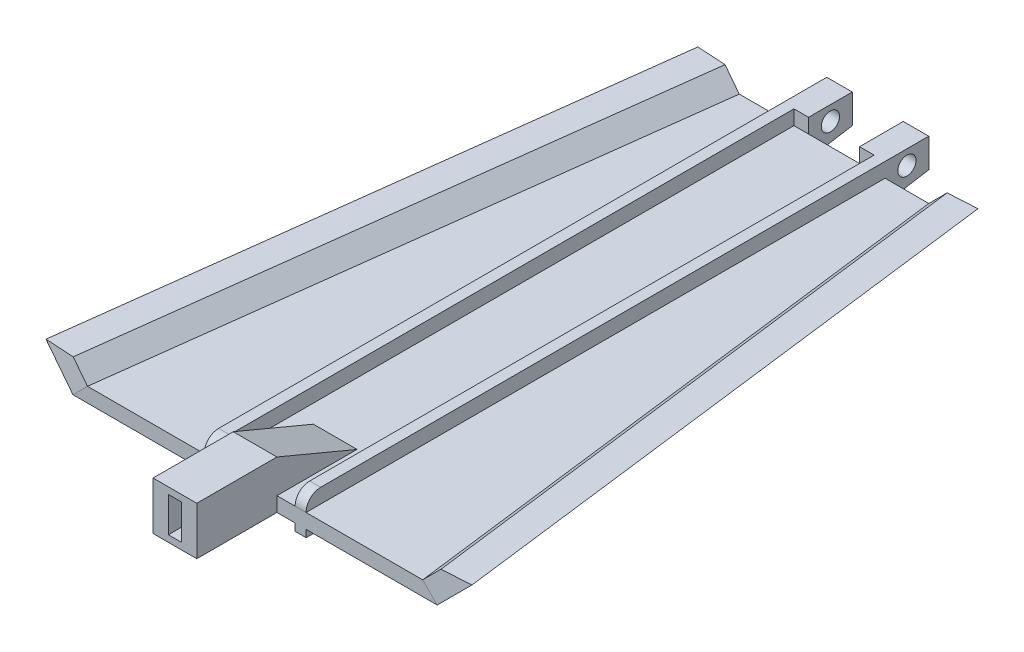
SolidWorks part; units mm, degrees
ref_plane "Front Plane" through (0, 0, 0) normal (0, 0, 1) x (1, 0, 0)
ref_plane "Top Plane" through (0, 0, 0) normal (0, 1, 0) x (1, 0, 0)
ref_plane "Right Plane" through (0, 0, 0) normal (1, 0, 0) x (0, 0, -1)
sketch "Sketch1" plane through (0, 0, 0) normal (0, 1, 0) x (1, 0, 0)
  line L4 (-21.0586, -39.6541) -> (28.9414, -39.6541)
  line L9 (-26.3294, 36.0752) -> (28.9414, -39.6541) construction
  line L10 (-21.0586, -39.6541) -> (22.9141, 43.1481) construction
  line L11 (28.9414, -39.6541) -> (18.9414, 39.805)
  line L12 (18.9414, 39.805) -> (-11.0586, 39.805)
  line L13 (-11.0586, 39.805) -> (-21.0586, -39.6541)
  point P0 (0, 0)
  dimension "D1" = 50
  dimension "D2" = 30
extrude "Boss-Extrude1" add sketch "Sketch1" along normal blind 2
sketch "Sketch2" plane through (0, 0, 39.6541) normal (0, 0, 1) x (1, 0, 0)
  line L0 (-21.0586, 2) -> (-21.0586, 0)
  line L1 (-21.0586, 0) -> (-19.0586, 2)
  line L2 (-21.0586, 2) -> (28.9414, 2) construction
  line L3 (-19.0586, 2) -> (-21.0586, 2)
sketch "Sketch3" plane through (0, 0, -39.805) normal (0, 0, -1) x (-1, 0, 0)
  line L2 (-18.9414, 2) -> (11.0586, 2) construction
  line L4 (11.0586, 0) -> (11.0586, 2)
  line L5 (11.0586, 2) -> (9.0586, 2)
  line L6 (9.0586, 2) -> (11.0586, 0)
  dimension "D2" = 2
loft "Cut-Loft1" cut profiles "Sketch2", "Sketch3"
sketch "Sketch4" plane through (0, 0, 39.6541) normal (0, 0, 1) x (1, 0, 0)
  line L0 (28.9414, 0) -> (28.9414, 2)
  line L1 (28.9414, 2) -> (26.9414, 2)
  line L2 (-19.0586, 2) -> (28.9414, 2) construction
  line L3 (26.9414, 2) -> (28.9414, 0)
  dimension "D1" = 2
sketch "Sketch5" plane through (0, 0, -39.805) normal (0, 0, -1) x (-1, 0, 0)
  line L0 (-18.9414, 0) -> (-18.9414, 2)
  line L1 (-18.9414, 2) -> (-16.9414, 2)
  line L2 (-18.9414, 2) -> (9.0586, 2) construction
  line L3 (-16.9414, 2) -> (-18.9414, 0)
  dimension "D1" = 2
loft "Cut-Loft2" cut profiles "Sketch5", "Sketch4"
sketch "Sketch6" plane through (11.8814, 11.8814, -1.4953) normal (0.7043, 0.7043, -0.0886) x (-0.0627, -0.0627, -0.9961)
  line L0 (-41.312, -20.4647) -> (38.4611, -13.3936)
  line L1 (38.4611, -13.3936) -> (38.4611, -10.5652)
  line L2 (38.4611, -10.5652) -> (-41.312, -17.6362)
  line L3 (-41.312, -17.6362) -> (-41.312, -20.4647)
extrude "Boss-Extrude2" add sketch "Sketch6" along normal blind 6
sketch "Sketch7" plane through (-7.9709, 7.9709, -1.0031) normal (-0.7043, 0.7043, -0.0886) x (-0.0627, 0.0627, 0.9961)
  line L0 (-38.9552, -4.9912) -> (40.8179, -12.0622)
  line L1 (40.8179, -12.0622) -> (40.8179, -14.8907)
  line L2 (40.8179, -14.8907) -> (-38.9552, -7.8196)
  line L3 (-38.9552, -7.8196) -> (-38.9552, -4.9912)
extrude "Boss-Extrude3" add sketch "Sketch7" along normal blind 6
sketch "Sketch8" plane through (-2.5584, 2.5584, 40.6573) normal (-0.0627, 0.0627, 0.9961) x (0.998, 0.0039, 0.0626)
  line L4 (-22.7709, 1.7607) -> (-18.7788, 1.7607)
  line L5 (-20.767, 3.7567) -> (-16.5327, -0.4943) construction
  line L6 (-18.7788, 1.7607) -> (-20.767, 3.7567)
  line L7 (-20.767, 3.7567) -> (-22.7709, 1.7607)
sketch "Sketch9" plane through (2.4416, -2.4416, -38.8019) normal (0.0627, -0.0627, -0.9961) x (-0.998, -0.0039, -0.0626)
  line L4 (17.7611, 6.7508) -> (13.7689, 6.7508)
  line L5 (15.7571, 8.7469) -> (11.5229, 4.4959) construction
  line L6 (13.7689, 6.7508) -> (15.7571, 8.7469)
  line L7 (15.7571, 8.7469) -> (17.7611, 6.7508) construction
  line L8 (15.7571, 8.7469) -> (17.7611, 6.7508)
loft "Cut-Loft3" cut profiles "Sketch9", "Sketch8"
sketch "Sketch12" plane through (-2.4107, -2.4107, -38.3097) normal (-0.0627, -0.0627, -0.9961) x (-0.998, 0.0039, 0.0626)
  line L0 (-25.6284, 6.7508) -> (-21.6363, 6.7508)
  line L1 (-23.6245, 8.7469) -> (-19.3902, 4.4959) construction
  line L2 (-21.6363, 6.7508) -> (-23.6245, 8.7469)
  line L3 (-23.6245, 8.7469) -> (-25.6284, 6.7508)
sketch "Sketch13" plane through (2.5893, 2.5893, 41.1494) normal (0.0627, 0.0627, 0.9961) x (0.998, -0.0039, -0.0626)
  line L0 (30.6383, 1.7607) -> (26.6461, 1.7607)
  line L1 (28.6343, 3.7567) -> (24.4, -0.4943) construction
  line L2 (26.6461, 1.7607) -> (28.6343, 3.7567)
  line L3 (28.6343, 3.7567) -> (30.6383, 1.7607)
loft "Cut-Loft4" cut profiles "Sketch13", "Sketch12"
sketch "Sketch14" plane through (0, 2, 0) normal (0, 1, 0) x (1, 0, 0)
  line L0 (3.9414, 39.805) -> (3.9414, -39.6541) construction
  line L1 (16.9414, 39.805) -> (-9.0586, 39.805) construction
  line L2 (-19.0586, -39.6541) -> (26.9414, -39.6541) construction
  line L3 (3.9414, 39.805) -> (9.4414, 39.805) construction
  line L4 (3.9414, 39.805) -> (-1.5586, 39.805) construction
  line L5 (9.4414, 39.805) -> (9.4414, -39.6541)
  line L6 (-1.5586, 39.805) -> (-1.5586, -39.6541)
  line L7 (-1.5586, -39.6541) -> (-3.0586, -39.6541)
  line L8 (-3.0586, -39.6541) -> (-3.0586, 39.805)
  line L9 (-3.0586, 39.805) -> (-1.5586, 39.805)
  line L10 (9.4414, 39.805) -> (10.9414, 39.805)
  line L11 (10.9414, 39.805) -> (10.9414, -39.6541)
  line L12 (10.9414, -39.6541) -> (9.4414, -39.6541)
  dimension "D1" = 5.5
  dimension "D2" = 1.5
  dimension "D3" = 1.5
extrude "Boss-Extrude4" add sketch "Sketch14" along normal blind 2
sketch "Sketch15" plane through (0, 0, 39.6541) normal (0, 0, 1) x (1, 0, 0)
  line L0 (3.9414, 0) -> (6.9414, 0)
  line L1 (-21.0586, 0) -> (28.9414, 0) construction
  line L2 (6.9414, 0) -> (6.9414, 6.6)
  line L3 (6.9414, 6.6) -> (0.9414, 6.6)
  line L4 (0.9414, 6.6) -> (0.9414, 0)
  line L5 (0.9414, 0) -> (3.9414, 0)
  dimension "D1" = 3
  dimension "D2" = 6.6
extrude "Boss-Extrude5" add sketch "Sketch15" along normal blind 11
sketch "Sketch19" plane through (0, 0, 50.6541) normal (0, 0, 1) x (1, 0, 0)
  line L0 (3.9414, 6.6) -> (3.9414, 0) construction
  line L1 (6.9414, 6.6) -> (0.9414, 6.6) construction
  line L2 (0.9414, 0) -> (6.9414, 0) construction
  line L4 (3.0414, 5.7) -> (4.8414, 5.7)
  line L5 (3.0414, 5.7) -> (3.0414, 0.9)
  line L6 (3.0414, 0.9) -> (4.8414, 0.9)
  line L7 (4.8414, 5.7) -> (4.8414, 0.9)
  line L8 (3.0414, 5.7) -> (4.8414, 0.9) construction
  line L9 (3.0414, 0.9) -> (4.8414, 5.7) construction
  point P6 (3.9414, 3.3)
  dimension "D1" = 4.8
  dimension "D2" = 1.8
extrude "Cut-Extrude2" cut sketch "Sketch19" against normal blind 11
sketch "Sketch20" plane through (0.9414, 0, 0) normal (-1, 0, 0) x (0, 0, 1)
  line L0 (39.6541, 2) -> (28.6541, 2)
  line L1 (28.6541, 2) -> (39.6541, 6.6)
  line L2 (39.6541, 6.6) -> (39.6541, 2)
extrude "Boss-Extrude7" add sketch "Sketch20" against normal blind 6
sketch "Sketch21" plane through (0, 0, -39.805) normal (0, 0, -1) x (-1, 0, 0)
  line L0 (-18.9414, 0) -> (11.0586, 0) construction
  line L1 (-10.9414, 4) -> (-9.4414, 4)
  line L2 (-10.9414, 4) -> (-10.9414, 0)
  line L3 (-10.9414, 0) -> (-9.4414, 0)
  line L4 (-9.4414, 4) -> (-9.4414, 0)
  line L6 (1.5586, 4) -> (3.0586, 4)
  line L7 (1.5586, 4) -> (1.5586, 0)
  line L8 (1.5586, 0) -> (3.0586, 0)
  line L9 (3.0586, 4) -> (3.0586, 0)
extrude "Boss-Extrude8" add sketch "Sketch21" along normal blind 6
sketch "Sketch24" plane through (-3.0586, 0, 0) normal (-1, 0, 0) x (0, 0, 1)
  line L1 (-39.805, 0) -> (-45.805, 0)
  line L2 (-39.805, 0) -> (-39.805, 4)
  line L3 (-39.805, 4) -> (-45.805, 4)
  line L4 (-45.805, 0) -> (-45.805, 4)
sketch "Sketch25" plane through (10.9414, 0, 0) normal (1, 0, 0) x (0, 0, -1)
  line L1 (39.805, 0) -> (45.805, 0)
  line L2 (39.805, 0) -> (39.805, 4)
  line L3 (39.805, 4) -> (45.805, 4)
  line L4 (45.805, 0) -> (45.805, 4)
sketch "Sketch22" plane through (10.9414, 0, 0) normal (1, 0, 0) x (0, 0, -1)
  line L0 (42.805, 0) -> (42.805, 4) construction
  line L1 (45.805, 0) -> (39.805, 0) construction
  line L2 (-39.6541, 4) -> (45.805, 4) construction
  circle A0 centre (42.805, 2) radius 1.25
  dimension "D1" = 2.5
extrude "Boss-Extrude9" add sketch "Sketch24" against normal blind 3.5
extrude "Boss-Extrude10" add sketch "Sketch25" against normal blind 3.5
extrude "Cut-Extrude3" cut sketch "Sketch22" against normal blind 23.5
sketch "Sketch27" plane through (0, 4, 0) normal (0, 1, 0) x (1, 0, 0)
  line L1 (-3.0586, -39.6541) -> (-1.5586, -39.6541)
  line L2 (-3.0586, -39.6541) -> (-3.0586, 39.805)
  line L3 (-3.0586, 39.805) -> (-1.5586, 39.805)
  line L4 (-1.5586, -39.6541) -> (-1.5586, 39.805)
  line L5 (9.4414, 39.805) -> (10.9414, 39.805)
  line L6 (9.4414, 39.805) -> (9.4414, -39.6541)
  line L7 (9.4414, -39.6541) -> (10.9414, -39.6541)
  line L8 (10.9414, 39.805) -> (10.9414, -39.6541)
extrude "Boss-Extrude11" add sketch "Sketch27" against normal blind 5
sketch "Sketch28" plane through (-1.5586, 0, 0) normal (1, 0, 0) x (0, 0, -1)
  line L0 (39.805, -1) -> (39.805, 0)
  line L1 (39.805, 0) -> (45.8489, 0)
  line L2 (45.8489, 0) -> (39.805, -1)
extrude "Boss-Extrude12" add sketch "Sketch28" along normal blind 2 and the other way blind 1.5
sketch "Sketch29" plane through (10.9414, 0, 0) normal (1, 0, 0) x (0, 0, -1)
  line L0 (39.805, 0) -> (45.805, 0)
  line L1 (45.805, 0) -> (39.805, -1)
  line L2 (39.805, -1) -> (39.805, 0)
extrude "Boss-Extrude13" add sketch "Sketch29" against normal blind 3.5
sketch "Sketch31" plane through (-1.5586, 0, 0) normal (1, 0, 0) x (0, 0, -1)
  line L0 (39.805, -1) -> (35.805, 0)
  line L1 (-39.6541, 0) -> (39.805, 0) construction
  line L2 (35.805, 0) -> (39.805, 0)
  line L3 (39.805, 0) -> (39.805, -1)
  dimension "D1" = 4
extrude "Boss-Extrude14" add sketch "Sketch31" along normal blind 2
sketch "Sketch32" plane through (9.4414, 0, 0) normal (-1, 0, 0) x (0, 0, 1)
  line L0 (-39.805, 0) -> (-39.805, -1)
  line L1 (-39.805, -1) -> (-35.805, 0)
  line L2 (-39.805, 0) -> (39.6541, 0) construction
  line L3 (-35.805, 0) -> (-39.805, 0)
  dimension "D1" = 4
extrude "Boss-Extrude15" add sketch "Sketch32" along normal blind 2
fillet "Fillet2" radius 2 2 edges at (10.1914, 4, 39.6541) (-2.3086, 4, 39.6541)
